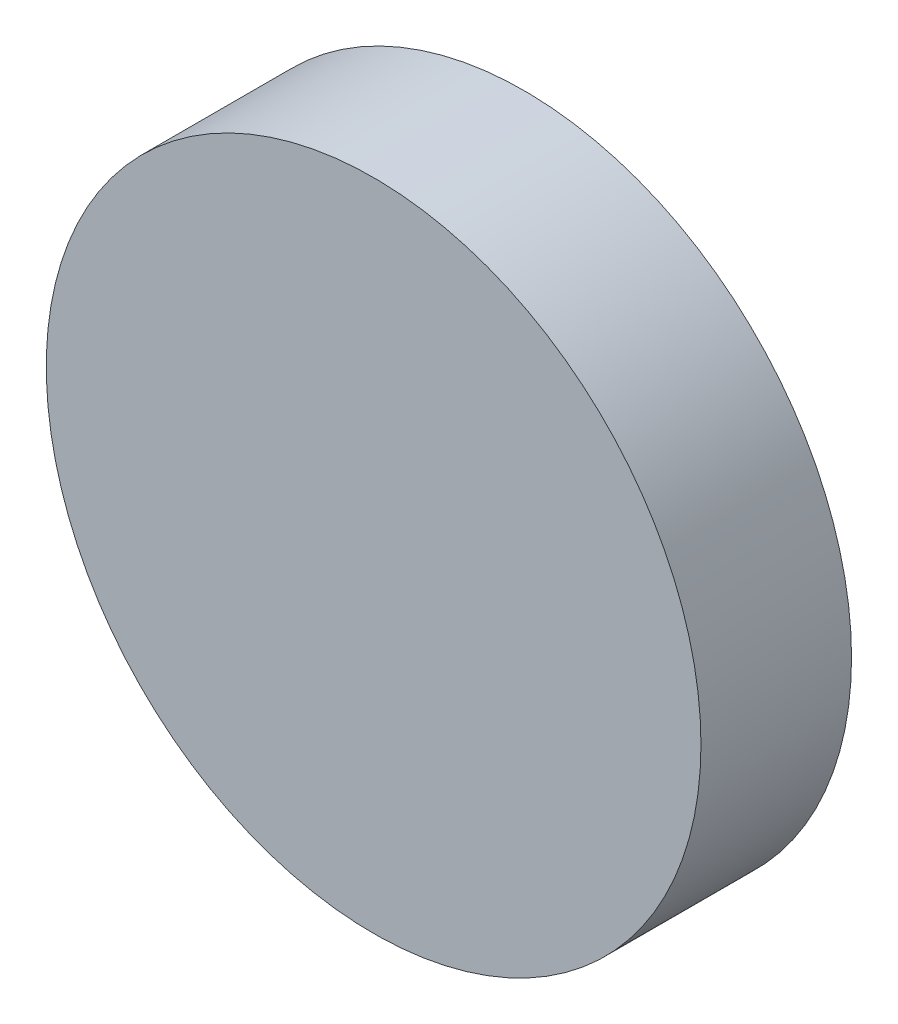
SolidWorks part; units mm, degrees
ref_plane "前视基准面" through (0, 0, 0) normal (0, 0, 1) x (1, 0, 0)
ref_plane "上视基准面" through (0, 0, 0) normal (0, 1, 0) x (1, 0, 0)
ref_plane "右视基准面" through (0, 0, 0) normal (1, 0, 0) x (0, 0, -1)
sketch "草图1" plane through (0, 0, 0) normal (0, 0, 1) x (1, 0, 0)
  circle A0 centre (40.4992, 24.6253) radius 5
  dimension "D1" = 10
extrude "凸台-拉伸1" add sketch "草图1" along normal blind 2.3
